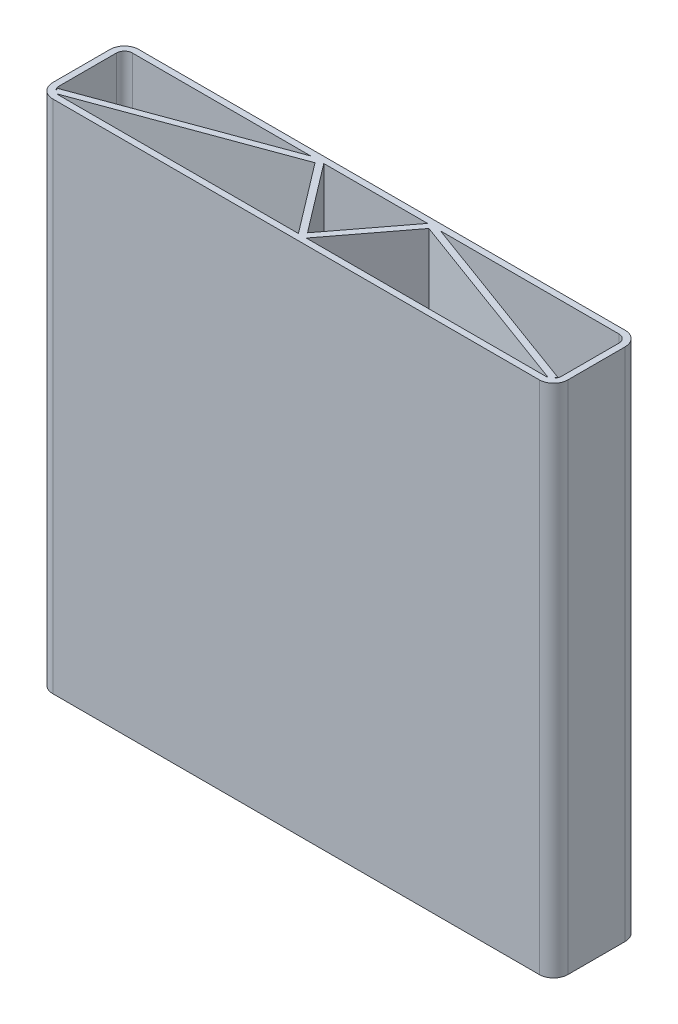
SolidWorks part; units mm, degrees
ref_plane "Front Plane" through (0, 0, 0) normal (0, 0, 1) x (1, 0, 0)
ref_plane "Top Plane" through (0, 0, 0) normal (0, 1, 0) x (1, 0, 0)
ref_plane "Right Plane" through (0, 0, 0) normal (1, 0, 0) x (0, 0, -1)
sketch "Sketch1" plane through (0, 0, 0) normal (0, 1, 0) x (1, 0, 0)
  line L1 (-863.6, 152.4) -> (863.6, 152.4)
  line L2 (-914.4, 101.6) -> (-914.4, -101.6)
  line L3 (-863.6, -152.4) -> (863.6, -152.4)
  line L4 (914.4, 101.6) -> (914.4, -101.6)
  line L5 (-914.4, 152.4) -> (914.4, -152.4) construction
  line L6 (-914.4, -152.4) -> (914.4, 152.4) construction
  arc A0 (863.6, 152.4) -> (914.4, 101.6) centre (863.6, 101.6) cw
  arc A1 (863.6, -152.4) -> (914.4, -101.6) centre (863.6, -101.6) ccw
  arc A2 (-914.4, -101.6) -> (-863.6, -152.4) centre (-863.6, -101.6) ccw
  arc A3 (-863.6, 152.4) -> (-914.4, 101.6) centre (-863.6, 101.6) ccw
  point P0 (0, 0)
  dimension "D3" = 50.8
  dimension "D1" = 1828.8
  dimension "D2" = 304.8
extrude "Extrude-Thin1" add sketch "Sketch1" along normal blind 1828.8 thin
sketch "Sketch2" plane through (0, 1828.8, 0) normal (0, 1, 0) x (1, 0, 0)
  line L0 (-883.8056, -121.8056) -> (-198.1098, 130.175)
  line L1 (863.6, 130.175) -> (-863.6, 130.175) construction
  line L3 (-198.1098, 130.175) -> (0, -130.175)
  line L4 (-863.6, -130.175) -> (863.6, -130.175) construction
  line L6 (0, -130.175) -> (198.1098, 130.175)
  line L7 (198.1098, 130.175) -> (883.8056, -121.8056)
  arc A0 (-892.175, -101.6) -> (-863.6, -130.175) centre (-863.6, -101.6) ccw construction
  arc A1 (863.6, -130.175) -> (892.175, -101.6) centre (863.6, -101.6) ccw construction
extrude "Extrude-Thin3" add sketch "Sketch2" against normal up to vertex (1828.8 mm away) thin thin type mid plane wall 22.225
